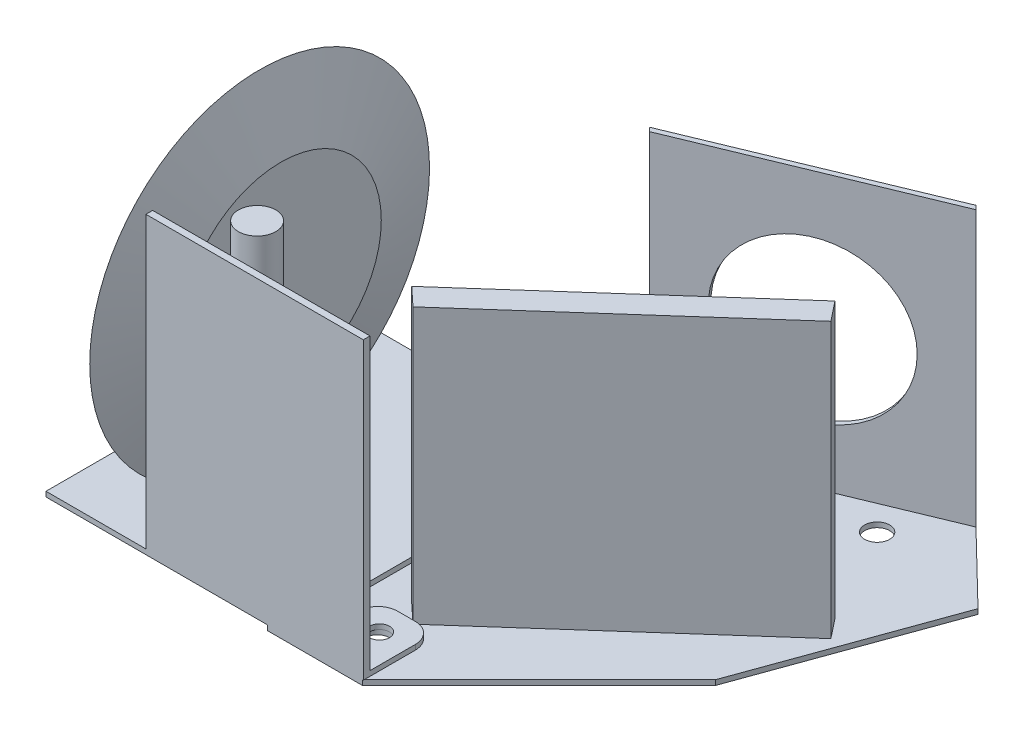
SolidWorks part; units mm, degrees
ref_plane "Alzado" through (0, 0, 0) normal (0, 0, 1) x (1, 0, 0)
ref_plane "Planta" through (0, 0, 0) normal (0, 1, 0) x (1, 0, 0)
ref_plane "Vista lateral" through (0, 0, 0) normal (1, 0, 0) x (0, 0, -1)
sketch "Croquis1" plane through (0, 0, 0) normal (0, 1, 0) x (1, 0, 0)
  line L0 (57.75, 14.4) -> (57.75, 8.9868) construction
  line L1 (0, 0) -> (48, 0)
  line L2 (0, 0) -> (0, 61)
  line L3 (0, 61) -> (43.4174, 61)
  line L4 (48, 5.7871) -> (48, 58)
  line L5 (53, 0) -> (63.5, 0)
  line L6 (52, 5.7871) -> (52, 10.4)
  line L7 (56, 14.4) -> (59.5, 14.4)
  line L8 (63.5, 0) -> (63.5, 10.4)
  line L10 (53, 0) -> (48, 0)
  line L12 (52, 5.7871) -> (48, 5.7871)
  circle A0 centre (48, 63) radius 2
  circle A1 centre (57.75, 8.9868) radius 2
  arc A2 (59.5, 14.4) -> (63.5, 10.4) centre (59.5, 10.4) cw
  arc A3 (52, 10.4) -> (56, 14.4) centre (56, 10.4) cw
  arc A4 (48, 58) -> (43.4174, 61) centre (48, 63) ccw
  point P15 (63.5, 14.4)
  dimension "D3" = 4
  dimension "D6" = 4
  dimension "D7" = 4
  dimension "D10" = 10
  dimension "D2" = 48
  dimension "D4" = 61
  dimension "D5" = 14.4
  dimension "D8" = 11.5
  dimension "D9" = 4
extrude "Saliente-Extruir1" add sketch "Croquis1" along normal blind 1
sketch "Croquis2" plane through (0, 1, 0) normal (0, 1, 0) x (1, 0, 0)
  line L1 (63.5, 0) -> (20, 0)
  line L2 (63.5, 0) -> (63.5, 1.3393)
  line L3 (63.5, 1.3393) -> (20, 1.3393)
  line L4 (20, 0) -> (20, 1.3393)
  dimension "D1" = 43.5
extrude "Saliente-Extruir2" add sketch "Croquis2" along normal blind 58
sketch "Croquis3" plane through (0, 0, 0) normal (0, -1, 0) x (-1, 0, 0)
  line L0 (-44.3009, 65.5) -> (-44.3009, 0)
  line L1 (-44.3009, 65.5) -> (-98.2554, 87.8487)
  line L2 (-44.3009, 0) -> (-63.3009, 0)
  line L3 (-63.3009, 0) -> (-98.6562, 35.3553)
  line L4 (-44.3009, 65.5) -> (-67.3228, 65.5) construction
  line L5 (-98.2554, 87.8487) -> (-112.5996, 73.9116)
  line L6 (-112.5996, 73.9116) -> (-98.6562, 35.3553)
  line L8 (0, 0) -> (-63.5, 0) construction
  line L9 (0, 61) -> (0, 0) construction
  circle A0 centre (-57.8009, 8.5) radius 2.5
  circle A1 centre (-48.4406, 62.8801) radius 2.5
  circle A2 centre (-89.2467, 77.0816) radius 2.5
  dimension "D9" = 5
  dimension "D13" = 5
  dimension "D16" = 5
  dimension "D1" = 65.5
  dimension "D2" = 58.4
  dimension "D3" = 19
  dimension "D4" = 50
  dimension "D5" = 45
  dimension "D6" = 22.5
  dimension "D7" = 20
  dimension "D8" = 41
  dimension "D10" = 13.5
  dimension "D11" = 8.5
  dimension "D12" = 44.3009
  dimension "D14" = 4.1397
  dimension "D15" = 62.8801
  dimension "D17" = 6.5
  dimension "D18" = 14
extrude "Saliente-Extruir3" add sketch "Croquis3" along normal blind 1
sketch "Croquis4" plane through (0, 0, 0) normal (0, 1, 0) x (1, 0, 0)
  line L0 (51.2804, 69.4734) -> (97.4744, 88.6076)
  line L1 (49.6555, 67.718) -> (98.2554, 87.8487) construction
  line L2 (98.2554, 87.8487) -> (112.5996, 73.9116) construction
  line L3 (98.2554, 87.8487) -> (52.0614, 68.7145)
  line L4 (52.0614, 68.7145) -> (51.2804, 69.4734)
  line L5 (98.2554, 87.8487) -> (97.4744, 88.6076)
  dimension "D1" = 50
  dimension "D2" = 1
  dimension "D3" = 50
extrude "Saliente-Extruir4" add sketch "Croquis4" along normal blind 55 separate body
sketch "Croquis5" plane through (-16.67, 0, -40.245) normal (0.3827, 0, 0.9239) x (0.9239, 0, -0.3827)
  line L0 (99.3944, 55) -> (99.3944, 27.5) construction
  line L1 (74.3944, 55) -> (124.3944, 55) construction
  line L2 (124.3944, 27.5) -> (99.3944, 27.5) construction
  line L3 (124.3944, 55) -> (124.3944, 0) construction
  circle A0 centre (99.3944, 27.5) radius 16
  dimension "D1" = 32
extrude "Cortar-Extruir1" cut sketch "Croquis5" against normal blind 55
sketch "Croquis6" plane through (0, 0, 0) normal (0, 1, 0) x (1, 0, 0)
  line L0 (55.0824, 18.1066) -> (99.973, 57.9166)
  line L1 (58.7581, 14.6834) -> (103.0782, 53.9874)
  line L2 (55.0824, 18.1066) -> (58.7581, 14.6834)
  line L3 (99.973, 57.9166) -> (103.0782, 53.9874)
  dimension "D1" = 60
  dimension "D2" = 5
extrude "Saliente-Extruir5" add sketch "Croquis6" along normal blind 55
ref_plane "Plano1" through (10, 0, 0) normal (-1, 0, 0) x (0, 0, 1)
sketch "Croquis7" plane through (10, 0, 0) normal (-1, 0, 0) x (0, 0, 1)
  line L1 (-32.75, -1.3194) -> (-32.75, 37.1512) construction
  line L3 (-65.5, -1) -> (-65.5, 0) construction
  circle A0 centre (-32.75, 28.6806) radius 34
  point P9 (-65.5, -0.5)
  dimension "D3" = 68
  dimension "D1" = 32.75
  dimension "D2" = 30
extrude "Saliente-Extruir6" add sketch "Croquis7" along normal mid plane 8.5 draft 73
sketch "Croquis8" plane through (0, 1, 0) normal (0, 1, 0) x (1, 0, 0)
  line L0 (63.5, 1.3393) -> (63.5, 10.4) construction
  circle A0 centre (32.25, 10) radius 3.75
  dimension "D1" = 7.5
  dimension "D2" = 10
  dimension "D3" = 31.25
extrude "Saliente-Extruir7" add sketch "Croquis8" along normal up to surface (58 mm away) up to face at (41.75, 59, -0.6697)
